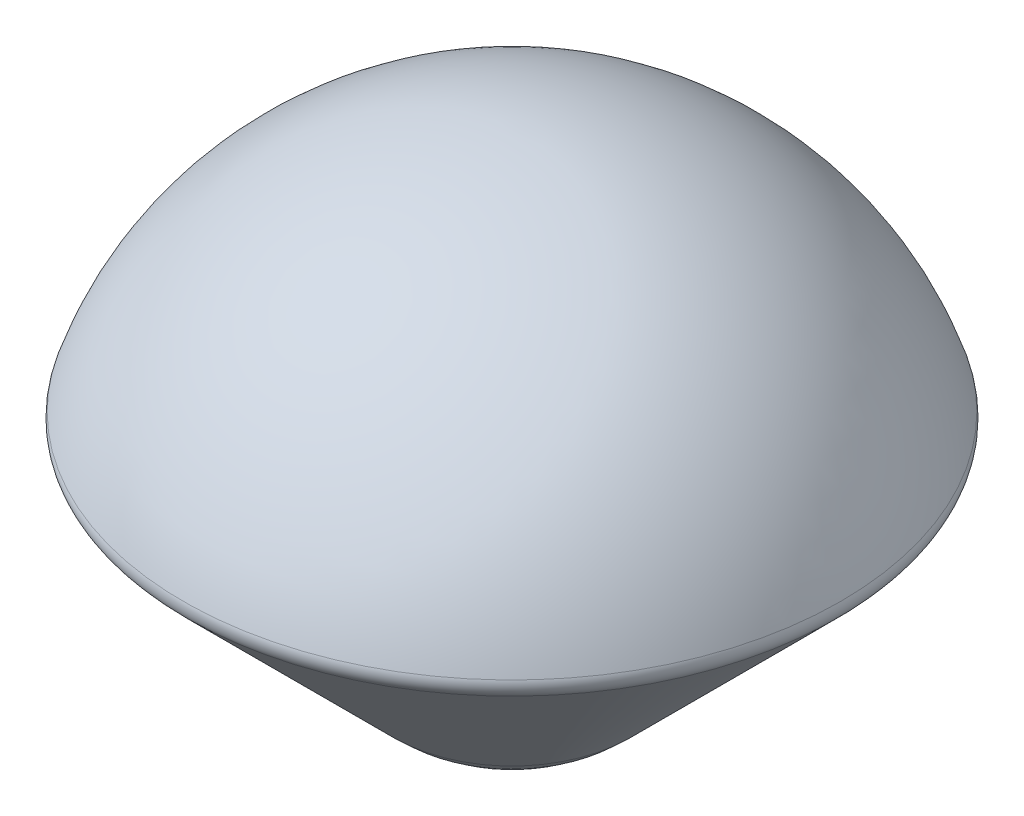
SolidWorks part; units mm, degrees
ref_plane "Front" through (0, 0, 0) normal (0, 0, 1) x (1, 0, 0)
ref_plane "Top" through (0, 0, 0) normal (0, 1, 0) x (1, 0, 0)
ref_plane "Right" through (0, 0, 0) normal (1, 0, 0) x (0, 0, -1)
sketch "Sketch3" plane through (0, 0, 0) normal (0, 0, 1) x (1, 0, 0)
  line L0 (0, 39.5461) -> (0, -37.5539)
  line L1 (49.9994, 2.0908) -> (-50.0006, 2.0908) construction
  line L2 (0, -12.5539) -> (17.7746, -30.1341) construction
  line L3 (0, -12.5539) -> (49.9994, 2.0908) construction
  line L4 (49.9994, 2.0908) -> (17.7746, -30.1341)
  arc A0 (0, 39.5461) -> (49.9994, 2.0908) centre (0, -12.5539) cw
  arc A1 (17.7746, -30.1341) -> (0, -37.5539) centre (0, -12.5539) cw
  dimension "D1" = 77.1
  dimension "D2" = 32.2249
  dimension "D3" = 17.5802
  dimension "D4" = 25
  dimension "D5" = 52.1
  dimension "D6" = 100
  dimension "D7" = 32.2249
revolve "Revolve3" add sketch "Sketch3" angle 360 about L0
fillet "Fillet1" radius 2.5 1 edges at (0, 2.0908, 49.9994)
